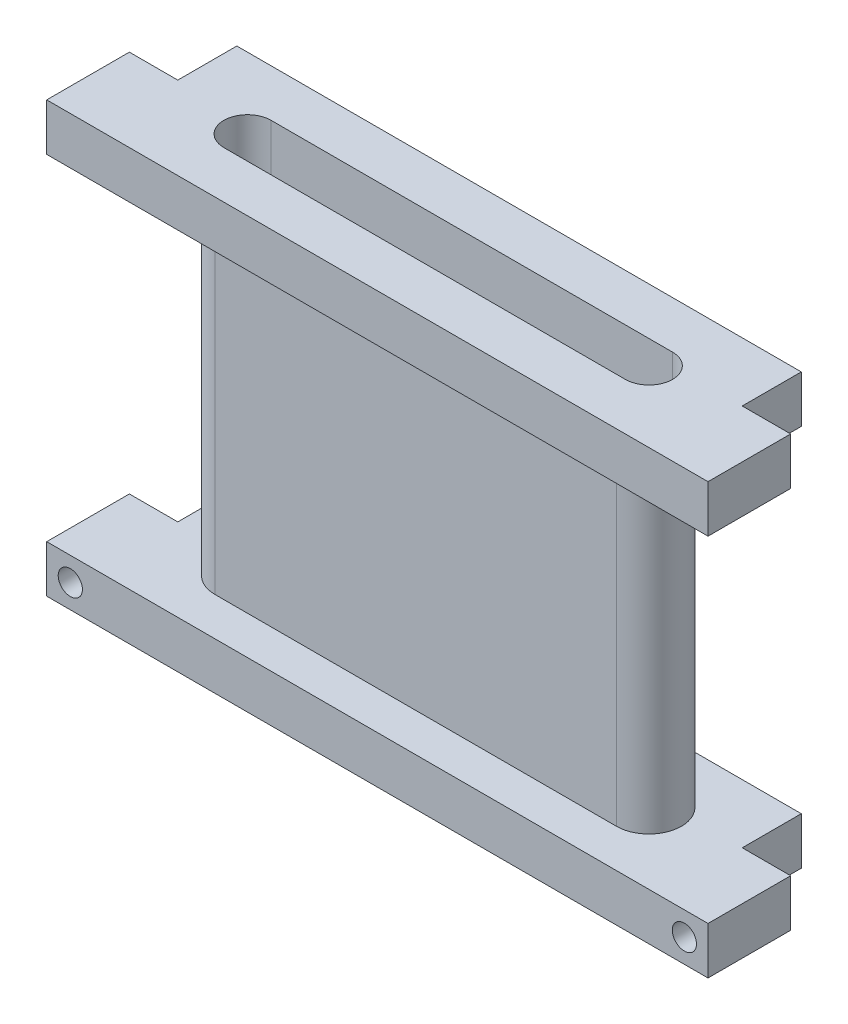
SolidWorks part; units mm, degrees
ref_plane "Front Plane" through (0, 0, 0) normal (0, 0, 1) x (1, 0, 0)
ref_plane "Top Plane" through (0, 0, 0) normal (0, 1, 0) x (1, 0, 0)
ref_plane "Right Plane" through (0, 0, 0) normal (1, 0, 0) x (0, 0, -1)
sketch "Sketch1" plane through (0, 0, 0) normal (0, 1, 0) x (1, 0, 0)
  line L0 (-28, 6) -> (-28, -2.75)
  line L1 (-28, -2.75) -> (28, -2.75)
  line L2 (28, -2.75) -> (28, 6)
  line L3 (28, 6) -> (-28, 6)
extrude "Boss-Extrude1" add sketch "Sketch1" against normal blind 4
sketch "Sketch2" plane through (0, 0, 0) normal (0, 1, 0) x (-1, 0, 0)
  line L0 (-17, 2.75) -> (17, 2.75)
  line L1 (17, -2.75) -> (-17, -2.75)
  arc A0 (-17, -2.75) -> (-17, 2.75) centre (-17, 0) cw
  arc A1 (17, 2.75) -> (17, -2.75) centre (17, 0) cw
extrude "Boss-Extrude2" add sketch "Sketch2" along normal blind 28.4
ref_plane "Plane1" through (0, 28.4, 0) normal (0, -1, 0) x (1, 0, 0)
sketch "Sketch3" plane through (0, 28.4, 0) normal (0, -1, 0) x (1, 0, 0)
  line L0 (28, 6) -> (-28, 6)
  line L1 (-28, 6) -> (-28, -6)
  line L2 (-28, -6) -> (28, -6)
  line L3 (28, -6) -> (28, 6)
extrude "Boss-Extrude3" add sketch "Sketch3" against normal blind 4
sketch "Sketch4" plane through (0, 0, 2.75) normal (0, 0, 1) x (1, 0, 0)
  line L0 (28, -4) -> (-28, -4)
  line L1 (-28, -4) -> (-28, 0)
  line L2 (-28, 0) -> (28, 0)
  line L3 (28, 0) -> (28, -4)
extrude "Boss-Extrude4" add sketch "Sketch4" along normal blind 3.25
sketch "Sketch5" plane through (0, 32.4, 0) normal (0, 1, 0) x (-1, 0, 0)
  line L0 (28, -1) -> (23.9, -1)
  line L1 (23.9, -1) -> (23.9, -6)
  line L2 (23.9, -6) -> (28, -6)
  line L3 (28, -6) -> (28, -1)
extrude "Cut-Extrude1" cut sketch "Sketch5" against normal up to next
sketch "Sketch6" plane through (0, 32.4, 0) normal (0, 1, 0) x (-1, 0, 0)
  line L0 (-23.9, -6) -> (-23.9, -1)
  line L1 (-23.9, -1) -> (-28, -1)
  line L2 (-28, -1) -> (-28, -6)
  line L3 (-28, -6) -> (-23.9, -6)
extrude "Cut-Extrude2" cut sketch "Sketch6" against normal up to next
sketch "Sketch7" plane through (0, -4, 0) normal (0, -1, 0) x (1, 0, 0)
  line L0 (23.9, -1) -> (23.9, -6)
  line L1 (23.9, -6) -> (28, -6)
  line L2 (28, -6) -> (28, -1)
  line L3 (28, -1) -> (23.9, -1)
extrude "Cut-Extrude3" cut sketch "Sketch7" against normal through all
sketch "Sketch8" plane through (0, -4, 0) normal (0, -1, 0) x (1, 0, 0)
  line L0 (-23.9, -6) -> (-23.9, -1)
  line L1 (-23.9, -1) -> (-28, -1)
  line L2 (-28, -1) -> (-28, -6)
  line L3 (-28, -6) -> (-23.9, -6)
extrude "Cut-Extrude4" cut sketch "Sketch8" against normal through all
sketch "Sketch9" plane through (0, -4, 0) normal (0, -1, 0) x (1, 0, 0)
  line L0 (-17, -2) -> (17, -2)
  line L1 (17, 2) -> (-17, 2)
  arc A0 (17, -2) -> (17, 2) centre (17, 0) ccw
  arc A1 (-17, 2) -> (-17, -2) centre (-17, 0) ccw
extrude "Cut-Extrude5" cut sketch "Sketch9" against normal through all
hole_wizard "Ø2.05 (2.05) Diameter Hole1" positions "Sketch11" profile "Sketch10" hole size "Ø2.05" standard "ANSI Metric"
sketch "Sketch11" plane through (0, 0, 6) normal (0, 0, 1) x (1, 0, 0)
  point P0 (26, -2)
  point P1 (-26, -2)
sketch "Sketch10" plane through (26, -2, 6) normal (1, 0, 0) x (0, -1, 0)
  line L0 (0, 0) -> (0, 4.6159)
  line L1 (0, 4.6159) -> (1.025, 4)
  line L2 (1.025, 4) -> (1.025, 0)
  line L5 (1.025, 0) -> (0, 0)
  line L10 (0, 4.6159) -> (-1.025, 4) construction
  line L11 (0, -6.35) -> (0, 107.95) construction
  dimension "Hole Dia." = 2.05
  dimension "Hole Depth" = 4
  dimension "Drill Angle" = 118
